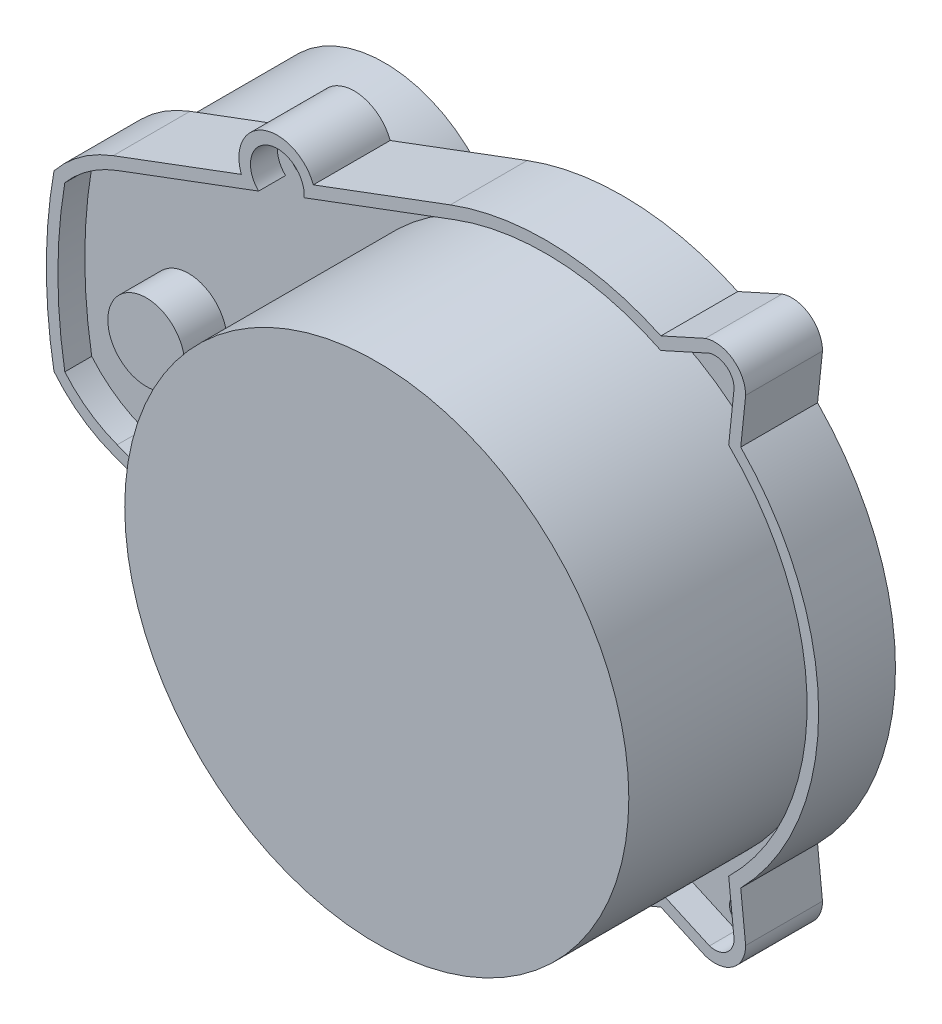
SolidWorks part; units mm, degrees
ref_plane "Plan de face" through (0, 0, 0) normal (0, 0, 1) x (1, 0, 0)
ref_plane "Plan de dessus" through (0, 0, 0) normal (0, 1, 0) x (1, 0, 0)
ref_plane "Plan de droite" through (0, 0, 0) normal (1, 0, 0) x (0, 0, -1)
sketch "Esquisse1" plane through (0, 0, 0) normal (0, 0, 1) x (1, 0, 0)
  line L0 (-12.425, 33.2546) -> (-30.2572, 26.5919)
  line L1 (-56.3, 16.8615) -> (-56.3, -16.8615) construction
  line L2 (-50, 0) -> (0, 0) construction
  line L3 (-12.425, 33.2546) -> (-12.425, -33.2546) construction
  line L5 (-35, 25) -> (-34.9409, 24.8419) construction
  line L6 (-39.6247, 23.0919) -> (-56.3, 16.8615)
  line L7 (-33.4505, 25.3988) -> (-36.4314, 24.2851)
  line L8 (20.756, 34.8016) -> (14.974, 32.1874)
  line L9 (26, 31) -> (25.36, 24.8419)
  line L10 (-65, 0) -> (35.5, 0) construction
  line L11 (55, 0) -> (-55, 0) construction
  line L12 (-35, -25) -> (-34.9409, -24.8419) construction
  line L13 (26, -31) -> (25.36, -24.8419)
  line L14 (20.756, -34.8016) -> (14.974, -32.1874)
  line L15 (-33.4505, -25.3988) -> (-36.4314, -24.2851)
  line L16 (-39.6247, -23.0919) -> (-56.3, -16.8615)
  line L17 (-12.425, -33.2546) -> (-30.2572, -26.5919)
  arc A1 (25.36, -24.8419) -> (25.36, 24.8419) centre (0, 0) ccw
  arc A3 (-64.01, 11.3013) -> (-64.01, -11.3013) centre (0, 0) ccw
  arc A4 (-56.3, 16.8615) -> (-64.01, 11.3013) centre (-50, 0) ccw
  circle A5 centre (22, 31) radius 1.6
  circle A6 centre (-35, 25) radius 1.6
  arc A7 (-30.2572, 26.5919) -> (-39.6247, 23.0919) centre (-34.9409, 24.8419) ccw
  arc A8 (26, 31) -> (20.756, 34.8016) centre (22, 31) ccw
  arc A9 (14.974, 32.1874) -> (-12.425, 33.2546) centre (0, 0) ccw
  arc A10 (14.974, -32.1874) -> (-12.425, -33.2546) centre (0, 0) cw
  arc A11 (26, -31) -> (20.756, -34.8016) centre (22, -31) cw
  arc A12 (-30.2572, -26.5919) -> (-39.6247, -23.0919) centre (-34.9409, -24.8419) cw
  circle A13 centre (-35, -25) radius 1.6
  circle A14 centre (22, -31) radius 1.6
  arc A15 (-56.3, -16.8615) -> (-64.01, -11.3013) centre (-50, 0) cw
  point P28 (-12.425, 0)
  point P29 (-56.3, 0)
  dimension "D1" = 71
  dimension "D4" = 130
  dimension "D6" = 3.2
  dimension "D10" = 10
  dimension "D11" = 8
  dimension "D3" = 50
  dimension "D5" = 31
  dimension "D7" = 22
  dimension "D8" = 35
  dimension "D9" = 25
extrude "Boss.-Extru.1" add sketch "Esquisse1" along normal blind 10 contours A15 L16 A12 L17 A10 L14 A11 L13 A1 L9 A8 L8 A9 L0 A7 L6 A4 A3 A13 A5 A6 A14
sketch "Esquisse2" plane through (0, 0, 10) normal (0, 0, 1) x (1, 0, 0)
  circle A0 centre (0, 0) radius 32.8
  dimension "D1" = 65.6
extrude "Boss.-Extru.2" add sketch "Esquisse2" along normal blind 22
sketch "Esquisse3" plane through (0, 0, 10) normal (0, 0, 1) x (1, 0, 0)
  line L16 (-55.775, -15.4564) -> (-37.3782, -22.33)
  line L17 (14.9568, -30.5335) -> (21.2911, -33.3974)
  line L18 (24.4991, -31.0687) -> (23.7942, -24.2866)
  line L19 (23.7942, 24.2866) -> (24.4991, 31.0687)
  line L20 (21.2911, 33.3974) -> (14.9568, 30.5335)
  line L21 (-11.9, 31.8495) -> (-31.4537, 24.5436)
  line L22 (-55.775, -15.4564) -> (-37.3782, -22.33)
  line L23 (14.9568, -30.5335) -> (21.2911, -33.3974)
  line L24 (24.4991, -31.0687) -> (23.7942, -24.2866)
  line L25 (23.7942, 24.2866) -> (24.4991, 31.0687)
  line L26 (21.2911, 33.3974) -> (14.9568, 30.5335)
  line L27 (-11.9, 31.8495) -> (-31.4537, 24.5436)
  line L28 (-31.4537, -24.5436) -> (-11.9, -31.8495)
  line L29 (-31.4537, -24.5436) -> (-11.9, -31.8495)
  line L30 (-37.3782, 22.33) -> (-55.775, 15.4564)
  line L31 (-37.3782, 22.33) -> (-55.775, 15.4564)
  arc A20 (-62.6, -10.6532) -> (-55.775, -15.4564) centre (-50, 0) ccw
  arc A21 (-11.9, -31.8495) -> (14.9568, -30.5335) centre (0, 0) ccw
  arc A22 (23.7942, -24.2866) -> (23.7942, 24.2866) centre (0, 0) ccw
  arc A23 (14.9568, 30.5335) -> (-11.9, 31.8495) centre (0, 0) ccw
  arc A24 (-55.775, 15.4564) -> (-62.6, 10.6532) centre (-50, 0) ccw
  arc A25 (-62.6, 10.6532) -> (-62.6, -10.6532) centre (0, 0) ccw
  arc A26 (-62.6, -10.6532) -> (-55.775, -15.4564) centre (-50, 0) ccw
  arc A27 (-11.9, -31.8495) -> (14.9568, -30.5335) centre (0, 0) ccw
  arc A28 (23.7942, -24.2866) -> (23.7942, 24.2866) centre (0, 0) ccw
  arc A29 (14.9568, 30.5335) -> (-11.9, 31.8495) centre (0, 0) ccw
  arc A30 (-55.775, 15.4564) -> (-62.6, 10.6532) centre (-50, 0) ccw
  arc A31 (-62.6, 10.6532) -> (-62.6, -10.6532) centre (0, 0) ccw
  arc A32 (-37.3782, -22.33) -> (-31.4537, -24.5436) centre (-34.9409, -24.8419) ccw
  arc A33 (-37.3782, -22.33) -> (-31.4537, -24.5436) centre (-34.9409, -24.8419) ccw
  arc A34 (21.2911, -33.3974) -> (24.4991, -31.0687) centre (22, -31) ccw
  arc A35 (21.2911, -33.3974) -> (24.4991, -31.0687) centre (22, -31) ccw
  arc A36 (24.4991, 31.0687) -> (21.2911, 33.3974) centre (22, 31) ccw
  arc A37 (24.4991, 31.0687) -> (21.2911, 33.3974) centre (22, 31) ccw
  arc A38 (-31.4537, 24.5436) -> (-37.3782, 22.33) centre (-34.9409, 24.8419) ccw
  arc A39 (-31.4537, 24.5436) -> (-37.3782, 22.33) centre (-34.9409, 24.8419) ccw
  dimension "D1" = 1.5
extrude "Enlèv. mat.-Extru.1" cut sketch "Esquisse3" against normal blind 3.5
sketch "Esquisse4" plane through (0, 0, 10) normal (0, 0, -1) x (-1, 0, 0)
  circle A1 centre (0, 0) radius 32.8
  circle A2 centre (0, 0) radius 32.8
  dimension "D1" = 0
extrude "Boss.-Extru.3" add sketch "Esquisse4" along normal up to next
sketch "Esquisse9" plane through (0, 0, 0) normal (0, 0, -1) x (-1, 0, 0)
  circle A0 centre (-22, -31) radius 1.6
  circle A1 centre (-22, 31) radius 1.6
  circle A2 centre (35, -25) radius 1.6
  circle A3 centre (35, 25) radius 1.6
  dimension "D1" = 62
  dimension "D2" = 57
  dimension "D3" = 57
  dimension "D4" = 50
sketch "Esquisse5" plane through (0, 0, 0) normal (0, 0, -1) x (-1, 0, 0)
  circle A0 centre (50, 0) radius 16
  dimension "D2" = 32
  dimension "D1" = 50
extrude "Boss.-Extru.4" add sketch "Esquisse5" along normal blind 19
ref_plane "Plan1" through (0, 0, -8) normal (0, 0, -1) x (-1, 0, 0)
sketch "Esquisse8" plane through (0, 0, 6.5) normal (0, 0, 1) x (1, 0, 0)
  circle A0 centre (-50, 0) radius 5
  dimension "D1" = 10
extrude "Boss.-Extru.7" add sketch "Esquisse8" along normal blind 5.5
